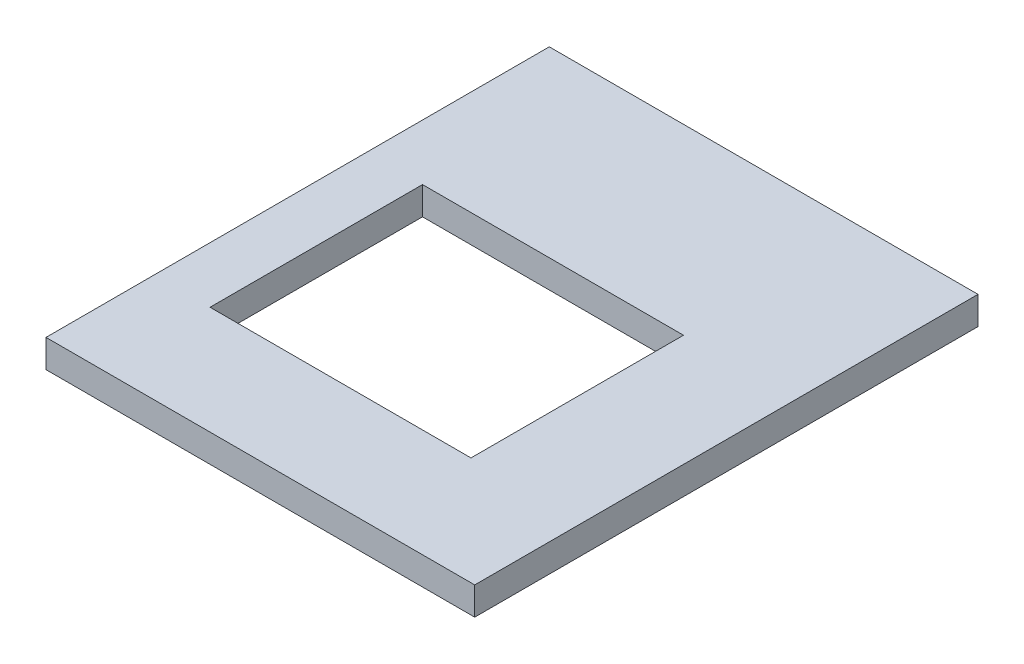
SolidWorks part; units mm, degrees
ref_plane "Plano frontal" through (0, 0, 0) normal (0, 0, 1) x (1, 0, 0)
ref_plane "Plano superior" through (0, 0, 0) normal (0, 1, 0) x (1, 0, 0)
ref_plane "Plano direito" through (0, 0, 0) normal (1, 0, 0) x (0, 0, -1)
sketch "Esboço1" plane through (0, 0, 0) normal (0, 0, 1) x (1, 0, 0)
  line L1 (0, 0) -> (2300, 0)
  line L2 (0, 0) -> (0, 150)
  line L3 (0, 150) -> (2300, 150)
  line L4 (2300, 0) -> (2300, 150)
  dimension "D1" = 150
  dimension "D2" = 2300
extrude "Ressalto-extrusão1" add sketch "Esboço1" along normal blind 2700
sketch "Esboço2" plane through (0, 150, 0) normal (0, 1, 0) x (1, 0, 0)
  line L1 (300, -980) -> (1700, -980)
  line L2 (300, -980) -> (300, -2120)
  line L3 (300, -2120) -> (1700, -2120)
  line L4 (1700, -980) -> (1700, -2120)
  line L6 (2300, 0) -> (0, 0) construction
  line L7 (2300, -2700) -> (2300, 0) construction
  dimension "D1" = 1400
  dimension "D2" = 600
  dimension "D3" = 1140
  dimension "D4" = 980
extrude "Corte-extrusão1" cut sketch "Esboço2" against normal through all
